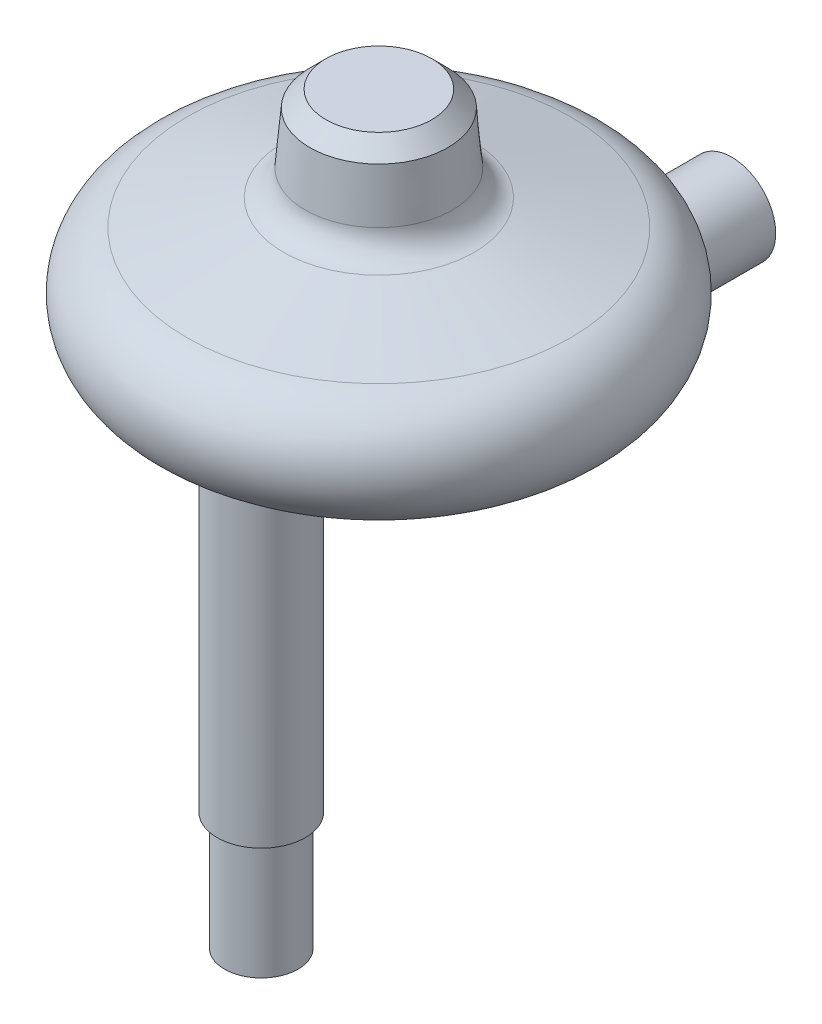
SolidWorks part; units mm, degrees
material "3003 Alloy"
ref_plane "Front" through (0, 0, 0) normal (0, 0, 1) x (1, 0, 0)
ref_plane "Top" through (0, 0, 0) normal (0, 1, 0) x (1, 0, 0)
ref_plane "Right" through (0, 0, 0) normal (1, 0, 0) x (0, 0, -1)
sketch "Sketch1" plane through (0, 0, 0) normal (0, 0, 1) x (1, 0, 0)
  line L0 (0, 0) -> (0, 69.3536) construction
  line L1 (0, 0) -> (19.05, 0)
  line L2 (20.6935, 12.4836) -> (0, 18.0284)
  line L4 (0, 18.0284) -> (0, 0)
  arc A0 (19.05, 0) -> (20.6935, 12.4836) centre (19.05, 6.35) ccw
  dimension "D2" = 6.35
  dimension "D1" = 50.8
  dimension "D3" = 15
revolve "Base-Revolve" add sketch "Sketch1" angle 360 about L0
sketch "Sketch2" plane through (0, 0, 0) normal (0, -1, 0) x (1, 0, 0)
  circle A0 centre (0, 0) radius 9.525
  dimension "D1" = 19.05
extrude "Boss-Extrude1" add sketch "Sketch2" against normal blind 25.4 draft 5
fillet "Fillet1" radius 3.175 1 edges at (0, 15.8477, 8.1385)
sketch "Sketch3" plane through (0, 0, 0) normal (0, -1, 0) x (1, 0, 0)
  circle A0 centre (0, 12.7) radius 4.7625
  dimension "D1" = 9.525
  dimension "D2" = 12.7
extrude "Boss-Extrude2" add sketch "Sketch3" along normal blind 35.875
fillet "Fillet2" radius 3.175 1 edges at (0, 0, 7.9375)
ref_plane "Plane4" through (0, 0, -6.35) normal (0, 0, 1) x (1, 0, 0)
sketch "Sketch4" plane through (0, 0, -6.35) normal (0, 0, 1) x (1, 0, 0)
  line L1 (-4.7625, 1.5875) -> (4.7625, 1.5875)
  line L2 (-4.7625, 1.5875) -> (-4.7625, -4.7625)
  line L3 (4.7625, -4.7625) -> (4.7625, 1.5875)
  line L4 (-19.05, 0) -> (19.05, 0) construction
  arc A0 (-4.7625, -4.7625) -> (4.7625, -4.7625) centre (0, -4.7625) ccw
  dimension "D1" = 4.7625
  dimension "D2" = 6.35
  dimension "D3" = 1.5875
extrude "Boss-Extrude3" add sketch "Sketch4" against normal blind 19.05
fillet "Fillet4" radius 1.5875 3 edges at (4.7625, -2.3812, -6.35) (-4.7625, -2.3812, -6.35) (0, -9.525, -6.35)
fillet "Fillet8" radius 1.5875 7 edges at (4.7625, 12.0396, -15.5158) (-4.7625, 12.5632, -17.0875) (4.7625, 0, -13.1913) (0, 0, -6.35) (-4.7625, 0, -13.1913) (4.2975, 0, -6.815) (-4.2975, 0, -6.815)
chamfer "Chamfer1" distance 1.5875 angle 45 1 edges at (0, 25.4, -7.3028)
sketch "Sketch5" plane through (0, 0, -25.4) normal (0, 0, -1) x (-1, 0, 0)
  circle A0 centre (0, -4.7625) radius 4.7625
  arc A1 (-4.7625, -4.7625) -> (4.7625, -4.7625) centre (0, -4.7625) ccw construction
extrude "Boss-Extrude4" add sketch "Sketch5" along normal blind 12.7
sketch "Sketch6" plane through (0, -35.875, 0) normal (0, -1, 0) x (1, 0, 0)
  circle A1 centre (0, 12.7) radius 3.9687
  circle A2 centre (0, 12.7) radius 3.9687
  dimension "D1" = 0.7937
extrude "Boss-Extrude5" add sketch "Sketch6" along normal blind 12.7
